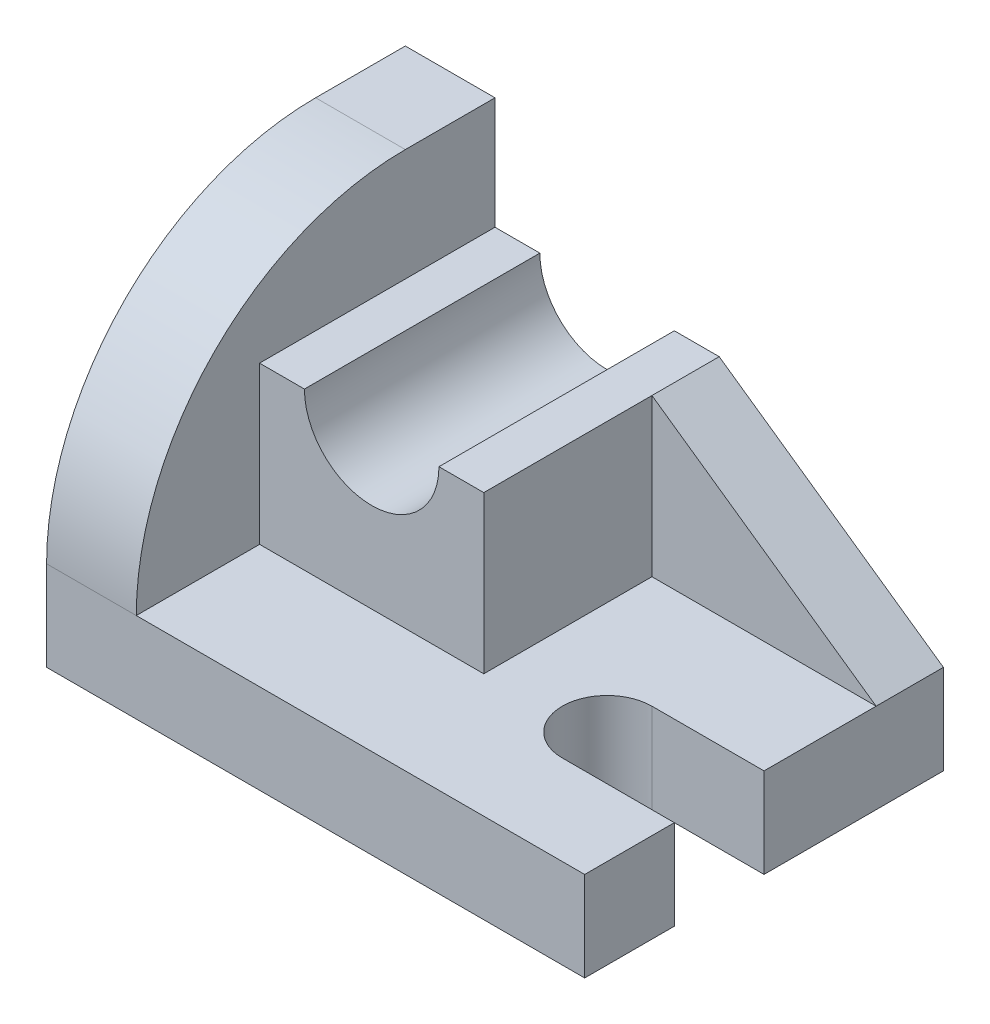
SolidWorks part; units mm, degrees
ref_plane "Front Plane" through (0, 0, 0) normal (0, 0, 1) x (1, 0, 0)
ref_plane "Top Plane" through (0, 0, 0) normal (0, 1, 0) x (1, 0, 0)
ref_plane "Right Plane" through (0, 0, 0) normal (1, 0, 0) x (0, 0, -1)
sketch "Sketch1" plane through (0, 0, 0) normal (0, 1, 0) x (1, 0, 0)
  line L1 (0, 0) -> (96, 0)
  line L2 (0, 0) -> (0, 64)
  line L3 (0, 64) -> (96, 64)
  line L4 (96, 0) -> (96, 64)
  dimension "D1" = 96
  dimension "D2" = 64
extrude "Boss-Extrude1" add sketch "Sketch1" along normal blind 16 contours L2 L3 L4 L1
sketch "Sketch2" plane through (0, 16, 0) normal (0, 1, 0) x (1, 0, 0)
  line L0 (96, 24) -> (76, 24) construction
  line L1 (96, 0) -> (96, 64) construction
  line L2 (96, 16) -> (76, 16)
  line L3 (96, 32) -> (76, 32)
  line L4 (0, 0) -> (96, 0) construction
  arc A0 (96, 16) -> (96, 32) centre (96, 24) ccw
  arc A1 (76, 32) -> (76, 16) centre (76, 24) ccw
  point P4 (86, 24)
  dimension "D3" = 16
  dimension "D1" = 8
  dimension "D2" = 20
extrude "Cut-Extrude1" cut sketch "Sketch2" against normal blind 16
sketch "Sketch3" plane through (0, 0, 0) normal (-1, 0, 0) x (0, 0, 1)
  line L1 (0, 0) -> (-64, 0)
  line L2 (0, 0) -> (0, 16)
  line L3 (-48, 64) -> (-64, 64)
  line L4 (-64, 0) -> (-64, 64)
  arc A0 (-48, 64) -> (0, 16) centre (-48, 16) cw
  point P7 (0, 64)
  dimension "D3" = 48
  dimension "D1" = 64
  dimension "D2" = 64
extrude "Boss-Extrude2" add sketch "Sketch3" against normal blind 16
sketch "Sketch4" plane through (0, 16, 0) normal (0, 1, 0) x (1, 0, 0)
  line L1 (16, 64) -> (56, 64)
  line L2 (16, 64) -> (16, 22)
  line L3 (16, 22) -> (56, 22)
  line L4 (56, 64) -> (56, 22)
  line L5 (16, 0) -> (96, 0) construction
  dimension "D1" = 40
  dimension "D2" = 22
extrude "Boss-Extrude3" add sketch "Sketch4" along normal blind 28
sketch "Sketch5" plane through (0, 0, -22) normal (0, 0, 1) x (1, 0, 0)
  line L0 (16, 44) -> (56, 44) construction
  circle A0 centre (36, 44) radius 12
  dimension "D1" = 24
extrude "Cut-Extrude2" cut sketch "Sketch5" against normal up to next
sketch "Sketch6" plane through (0, 0, -64) normal (0, 0, -1) x (-1, 0, 0)
  line L0 (-56, 44) -> (-96, 16)
  line L10 (-48, 44) -> (-56, 44)
  line L11 (-56, 44) -> (-56, 16)
  line L12 (-56, 16) -> (-96, 16)
  line L13 (-96, 16) -> (-96, 0)
  line L14 (-96, 0) -> (0, 0)
  line L15 (0, 0) -> (0, 64)
  line L16 (0, 64) -> (-16, 64)
  line L17 (-16, 64) -> (-16, 44)
  line L18 (-16, 44) -> (-24, 44)
  line L20 (-56, 44) -> (-56, 16)
  line L21 (-56, 16) -> (-96, 16)
  arc A1 (-48, 44) -> (-24, 44) centre (-36, 44) ccw
  dimension "D1" = 0
extrude "Boss-Extrude4" add sketch "Sketch6" against normal blind 12 separate body
